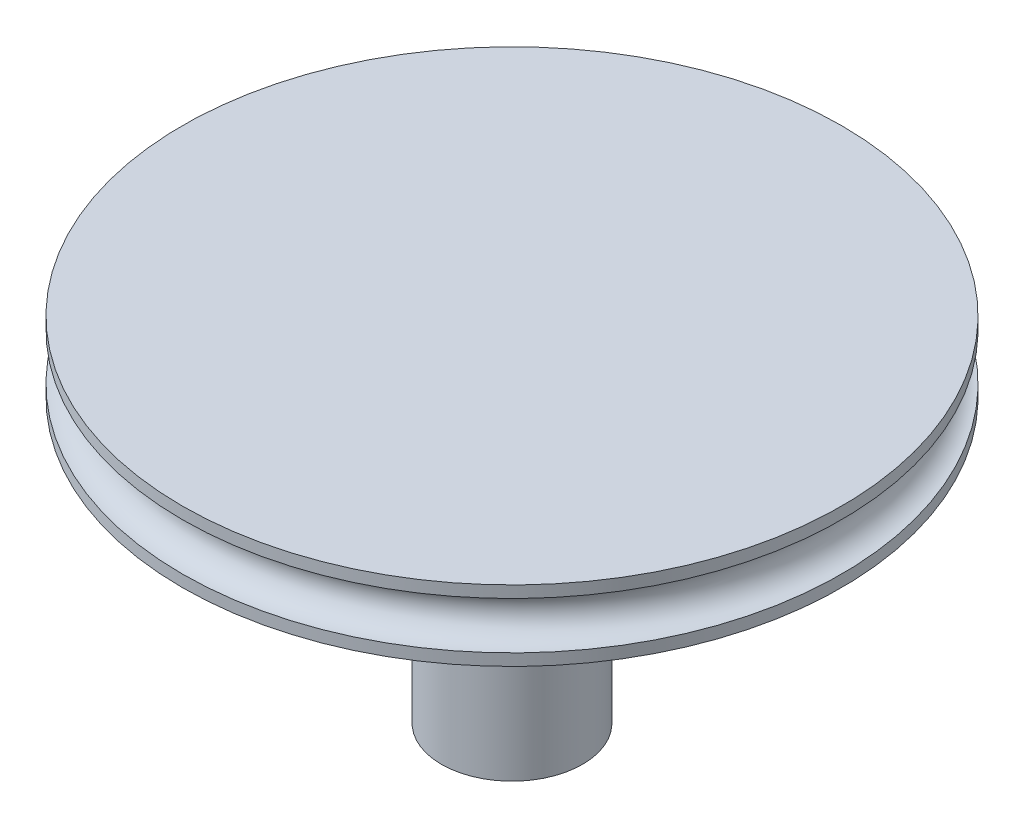
SolidWorks part; units mm, degrees
ref_plane "Front Plane" through (0, 0, 0) normal (0, 0, 1) x (1, 0, 0)
ref_plane "Top Plane" through (0, 0, 0) normal (0, 1, 0) x (1, 0, 0)
ref_plane "Right Plane" through (0, 0, 0) normal (1, 0, 0) x (0, 0, -1)
ref_axis "Axis1" through (0, 3.6, 0) along (0, -1, 0)
sketch "Sketch1" plane through (0, 0, 0) normal (0, 0, 1) x (1, 0, 0)
  line L0 (3, 0) -> (14, 0)
  line L1 (14, 3) -> (14, 2.5)
  line L2 (14, 3) -> (0, 3)
  line L3 (0, 3) -> (0, -12)
  line L4 (0, -12) -> (3, -12)
  line L5 (3, -12) -> (3, 0)
  line L6 (14, 0) -> (14, 0.5)
  arc A0 (14, 2.5) -> (14, 0.5) centre (14, 1.5) ccw
  dimension "D2" = 1
  dimension "D1" = 0.5
  dimension "D3" = 3
  dimension "D4" = 14
  dimension "D5" = 3
  dimension "D6" = 15
revolve "Revolve1" add sketch "Sketch1" angle 360 about axis through (0, 3.6, 0) along (0, -1, 0)
